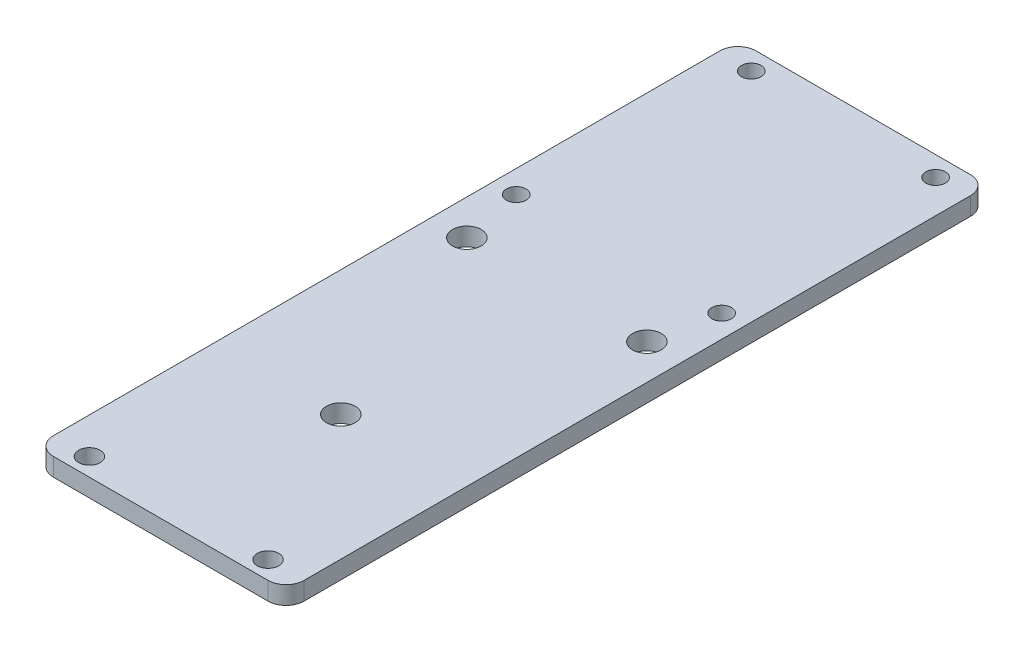
SolidWorks part; units mm, degrees
material "PPE"
ref_plane "Front Plane" through (0, 0, 0) normal (0, 0, 1) x (1, 0, 0)
ref_plane "Top Plane" through (0, 0, 0) normal (0, 1, 0) x (1, 0, 0)
ref_plane "Right Plane" through (0, 0, 0) normal (1, 0, 0) x (0, 0, -1)
sketch "Sketch1" plane through (0, 0, 0) normal (0, 1, 0) x (1, 0, 0)
  line L0 (-48.28, -100.5347) -> (-48.28, -94.1847) construction
  line L1 (9.375, -100.5347) -> (-34.825, -100.5347)
  line L2 (9.375, -100.5347) -> (9.375, 23.3453)
  line L3 (9.375, 23.3453) -> (-34.825, 23.3453)
  line L4 (-34.825, -100.5347) -> (-34.825, 23.3453)
  line L5 (6.1479, -100.5347) -> (-31.4789, -100.5347) construction
  line L6 (-34.825, -19.5547) -> (-34.825, -25.1547) construction
  line L7 (22.83, -100.5347) -> (22.83, -94.1847) construction
  line L8 (-32.475, 19.8453) -> (-32.475, -16.1547) construction
  line L9 (7.025, -16.1547) -> (7.025, 19.8453) construction
  line L10 (3.525, 23.3453) -> (-28.975, 23.3453) construction
  line L11 (-48.28, -100.5347) -> (-48.28, -94.1847) construction
  line L12 (22.83, -100.5347) -> (22.83, -94.1847) construction
  line L13 (-32.475, 19.8453) -> (-32.475, -16.1547) construction
  line L14 (7.025, -16.1547) -> (7.025, 19.8453) construction
  line L15 (3.525, 23.3453) -> (-28.975, 23.3453) construction
  line L16 (9.375, -25.1547) -> (9.375, -19.5547) construction
  line L17 (-34.825, -19.5547) -> (-34.825, -25.1547)
  line L18 (9.375, -25.1547) -> (9.375, -19.5547)
  circle A0 centre (-28.975, 19.8453) radius 1.2891 construction
  circle A1 centre (-28.975, 19.8453) radius 1.2891 construction
  circle A2 centre (3.525, 19.8453) radius 1.2891 construction
  circle A3 centre (3.525, 19.8453) radius 1.2891 construction
  point P0 (0, 0)
extrude "Boss-Extrude1" add sketch "Sketch1" along normal blind 3.175 contours L4 L1 L2 L3
hole_wizard "#5 Clearance Hole1" positions "Sketch3" profile "Sketch4" hole size "#5" standard "ANSI Inch" end condition through all
sketch "Sketch3" plane through (0, 0, 0) normal (0, -1, 0) x (-1, 0, 0)
  circle A0 centre (28.975, 19.8453) radius 1.2891 construction
  circle A1 centre (28.975, 19.8453) radius 1.2891
  circle A2 centre (-3.525, 19.8453) radius 1.2891 construction
  circle A3 centre (-3.525, 19.8453) radius 1.2891
  circle A4 centre (-5.3852, -19.7379) radius 1.2891 construction
  circle A5 centre (-5.3852, -19.7379) radius 1.2891
  circle A6 centre (30.8352, -19.7379) radius 1.2891 construction
  circle A7 centre (30.8352, -19.7379) radius 1.2891
  point P243 (28.975, 19.8453)
  point P245 (-3.525, 19.8453)
  point P247 (-5.3852, -19.7379)
  point P249 (30.8352, -19.7379)
sketch "Sketch4" plane through (-28.975, 0, -19.8453) normal (1, 0, 0) x (0, 0, -1)
  line L0 (0, 0) -> (0, 3.175)
  line L1 (0, 3.175) -> (1.7272, 3.175)
  line L2 (1.7272, 3.175) -> (1.7272, 0)
  line L5 (1.7272, 0) -> (0, 0)
  line L11 (0, -6.35) -> (0, 107.95) construction
  dimension "Thru Hole Dia." = 3.4544
  dimension "Thru Hole Depth" = 3.175
hole_wizard "#6 Clearance Hole1" positions "Sketch6" profile "Sketch5" hole size "#6" standard "ANSI Inch" end condition through all
sketch "Sketch6" plane through (0, 3.175, 0) normal (0, 1, 0) x (1, 0, 0)
  line L1 (3.025, -97.3597) -> (-28.475, -97.3597) construction
  line L3 (9.375, -100.5347) -> (-34.825, -100.5347) construction
  line L4 (9.375, -100.5347) -> (9.375, 23.3453) construction
  line L5 (-34.825, -100.5347) -> (-34.825, 23.3453) construction
  point P0 (3.025, -97.3597)
  point P2 (-28.475, -97.3597)
  dimension "D1" = 3.175
  dimension "D2" = 6.35
  dimension "D3" = 6.35
sketch "Sketch5" plane through (3.025, 3.175, 97.3597) normal (1, 0, 0) x (0, 0, 1)
  line L0 (0, 0) -> (0, 3.175)
  line L1 (0, 3.175) -> (1.8986, 3.175)
  line L2 (1.8986, 3.175) -> (1.8986, 0)
  line L5 (1.8986, 0) -> (0, 0)
  line L11 (0, -6.35) -> (0, 107.95) construction
  dimension "Thru Hole Dia." = 3.7973
  dimension "Thru Hole Depth" = 3.175
fillet "Fillet1" radius 3.175 4 edges at (9.375, 1.5875, 100.5347) (-34.825, 1.5875, 100.5347) (-34.825, 1.5875, -23.3453) (9.375, 1.5875, -23.3453)
hole_wizard "#8 (0.199) Diameter Hole1" positions "Sketch8" profile "Sketch7" hole size "#8" standard "ANSI Inch" end condition through all
sketch "Sketch8" plane through (0, 0, 0) normal (0, -1, 0) x (-1, 0, 0)
  line L0 (-3.15, -30.6847) -> (28.6, -30.6847) construction
  line L2 (-6.2, -100.5347) -> (31.65, -100.5347) construction
  line L3 (12.725, -30.6847) -> (12.725, -100.5347) construction
  point P0 (-3.15, -30.6847)
  point P2 (28.6, -30.6847)
  point P13 (12.725, -68.7847)
  dimension "D1" = 69.85
  dimension "D2" = 31.75
  dimension "D3" = 38.1
sketch "Sketch7" plane through (3.15, 0, 30.6847) normal (1, 0, 0) x (0, 0, -1)
  line L0 (0, 0) -> (0, 3.175)
  line L1 (0, 3.175) -> (2.5273, 3.175)
  line L2 (2.5273, 3.175) -> (2.5273, 0)
  line L5 (2.5273, 0) -> (0, 0)
  line L11 (0, -6.35) -> (0, 107.95) construction
  dimension "Thru Hole Dia." = 5.0546
  dimension "Thru Hole Depth" = 3.175
